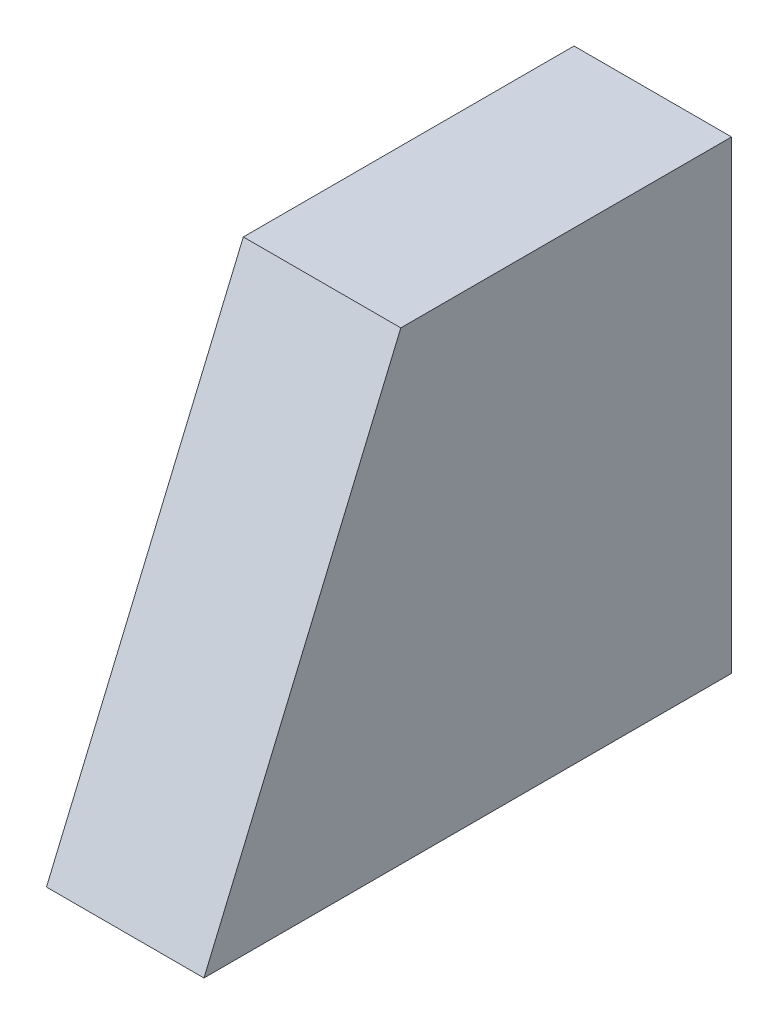
SolidWorks part; units mm, degrees
ref_plane "Front Plane" through (0, 0, 0) normal (0, 0, 1) x (1, 0, 0)
ref_plane "Top Plane" through (0, 0, 0) normal (0, 1, 0) x (1, 0, 0)
ref_plane "Right Plane" through (0, 0, 0) normal (1, 0, 0) x (0, 0, -1)
sketch "Sketch1" plane through (0, 0, 0) normal (1, 0, 0) x (0, 0, -1)
  line L0 (0, 0) -> (0, 295)
  line L1 (0, 295) -> (-210, 295)
  line L2 (-210, 295) -> (-335, 0)
  line L3 (-335, 0) -> (0, 0)
  dimension "D1" = 295
  dimension "D2" = 210
  dimension "D3" = 335
extrude "Boss-Extrude1" add sketch "Sketch1" along normal blind 100
